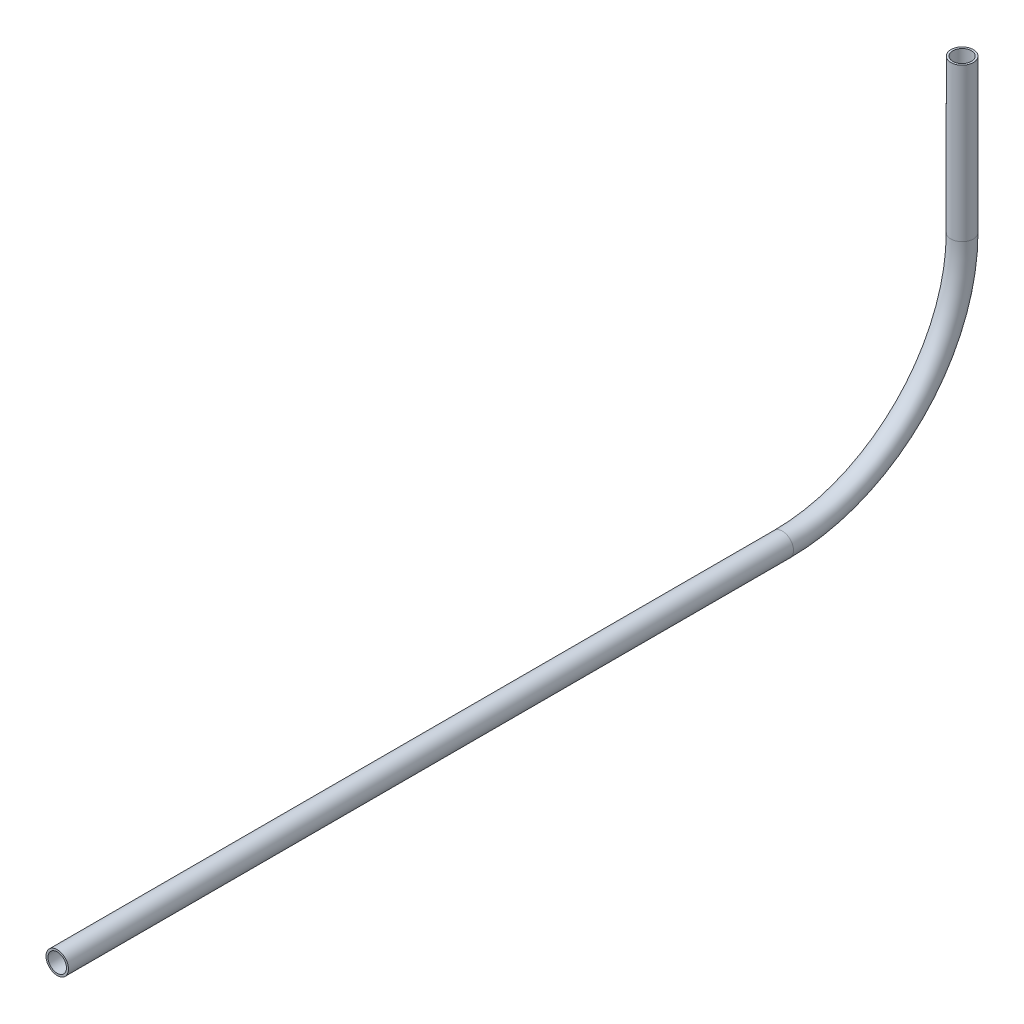
SolidWorks part; units mm, degrees
ref_plane "Front Plane" through (0, 0, 0) normal (0, 0, 1) x (1, 0, 0)
ref_plane "Top Plane" through (0, 0, 0) normal (0, 1, 0) x (1, 0, 0)
ref_plane "Right Plane" through (0, 0, 0) normal (1, 0, 0) x (0, 0, -1)
sketch "Sketch1" plane through (0, 0, 0) normal (1, 0, 0) x (0, 0, -1)
  line L0 (-258.9953, 165.1696) -> (-54.1651, 165.1696)
  line L1 (-3.3651, 215.9696) -> (-3.3651, 259.1446)
  arc A0 (-54.1651, 165.1696) -> (-3.3651, 215.9696) centre (-54.1651, 215.9696) ccw
  point P2 (-265.8046, 151.4238)
  point P6 (0, 0)
  point P7 (-3.3651, 206.2734)
  point P8 (0, 0)
  point P9 (-283.7187, 131.1445)
  point P10 (-281.537, 148.0663)
  point P11 (-269.5254, 169.7009)
  point P12 (-282.0276, 101.817)
  point P13 (-275.6102, 172.7053)
  point P14 (-272.6104, 164.8577)
  point P15 (0, 0)
  point P16 (-258.9953, 165.1696)
  dimension "D1" = 50.8
other "Pipe 0.5 SCH 40(1)"
ref_plane "Plane1" through (0, 165.1696, 258.9953) normal (0, 0, -1) x (0, 1, 0)
sketch "Sketch11" plane through (0, 165.1696, 258.9953) normal (0, 0, -1) x (0, 1, 0)
  circle A0 centre (0, 0) radius 3.175
  circle A1 centre (0, 0) radius 2.6162
  point P5 (0, 0)
  dimension "In_dia" = 6.35
  dimension "Out_dia" = 5.2324
